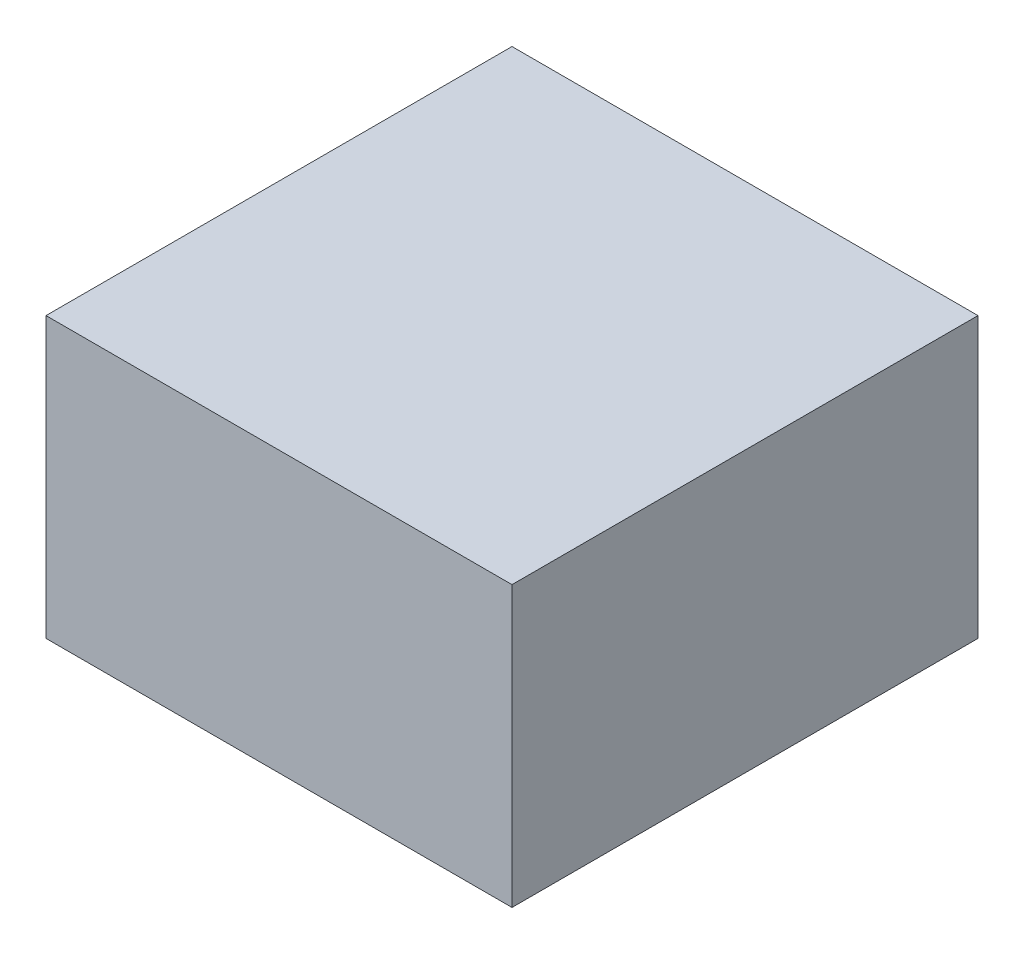
SolidWorks part; units mm, degrees
ref_plane "Front Plane" through (0, 0, 0) normal (0, 0, 1) x (1, 0, 0)
ref_plane "Top Plane" through (0, 0, 0) normal (0, 1, 0) x (1, 0, 0)
ref_plane "Right Plane" through (0, 0, 0) normal (1, 0, 0) x (0, 0, -1)
sketch "Sketch1" plane through (0, 0, 0) normal (0, 1, 0) x (1, 0, 0)
  line L1 (-31.75, 31.75) -> (31.75, 31.75)
  line L2 (-31.75, 31.75) -> (-31.75, -31.75)
  line L3 (-31.75, -31.75) -> (31.75, -31.75)
  line L4 (31.75, 31.75) -> (31.75, -31.75)
  line L5 (-31.75, 31.75) -> (31.75, -31.75) construction
  line L6 (-31.75, -31.75) -> (31.75, 31.75) construction
  point P0 (0, 0)
  dimension "D1" = 63.5
  dimension "D2" = 63.5
extrude "Boss-Extrude1" add sketch "Sketch1" along normal blind 38.1
